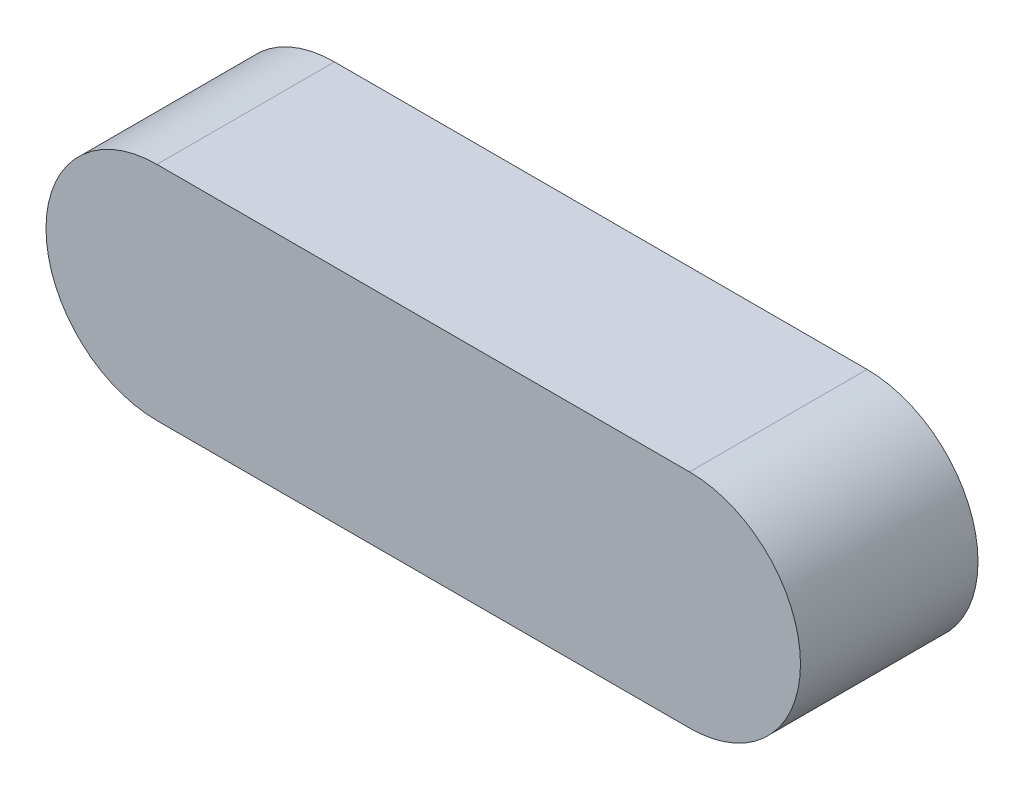
SolidWorks part; units mm, degrees
ref_plane "Front Plane" through (0, 0, 0) normal (0, 0, 1) x (1, 0, 0)
ref_plane "Top Plane" through (0, 0, 0) normal (0, 1, 0) x (1, 0, 0)
ref_plane "Right Plane" through (0, 0, 0) normal (1, 0, 0) x (0, 0, -1)
sketch "Sketch1" plane through (0, 0, 0) normal (0, 0, 1) x (1, 0, 0)
  line L0 (-76.2, 0) -> (76.2, 0) construction
  line L1 (-76.2, 31.75) -> (76.2, 31.75)
  line L2 (-76.2, -31.75) -> (76.2, -31.75)
  arc A0 (-76.2, 31.75) -> (-76.2, -31.75) centre (-76.2, 0) ccw
  arc A1 (76.2, -31.75) -> (76.2, 31.75) centre (76.2, 0) ccw
  point P2 (0, 0)
  dimension "D1" = 31.75
  dimension "D2" = 152.4
extrude "Boss-Extrude1" add sketch "Sketch1" along normal blind 50.8
